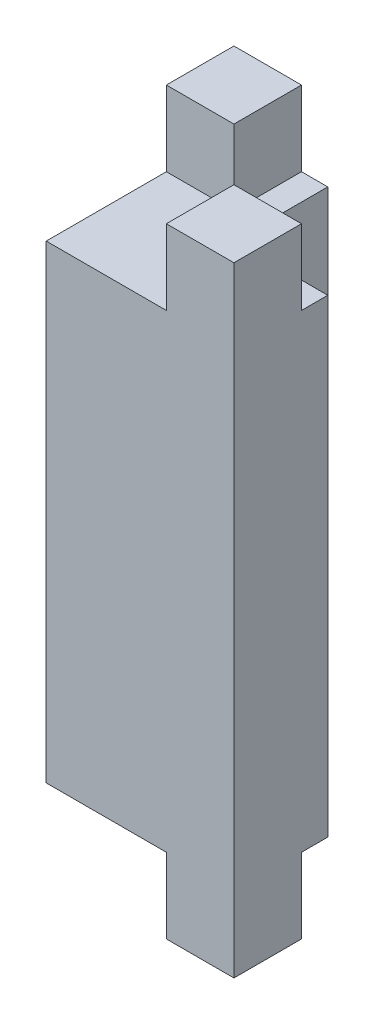
SolidWorks part; units mm, degrees
ref_plane "Front Plane" through (0, 0, 0) normal (0, 0, 1) x (1, 0, 0)
ref_plane "Top Plane" through (0, 0, 0) normal (0, 1, 0) x (1, 0, 0)
ref_plane "Right Plane" through (0, 0, 0) normal (1, 0, 0) x (0, 0, -1)
sketch "Sketch12" plane through (0, 0, 0) normal (0, 1, 0) x (1, 0, 0)
  line L0 (-5, -5) -> (5, -5)
  line L1 (-5, -5) -> (-5, 0)
  line L2 (0, 0) -> (5, 0)
  line L3 (5, -5) -> (5, 0)
  line L4 (-5, 0) -> (-5, 5)
  line L5 (-5, 5) -> (0, 5)
  line L6 (0, 0) -> (0, 5)
  dimension "D1" = 5
  dimension "D2" = 10
  dimension "D3" = 5
  dimension "D4" = 5
extrude "Boss-Extrude2" add sketch "Sketch12" along normal blind 25
sketch "Sketch13" plane through (0, 0, 0) normal (0, 1, 0) x (1, 0, 0)
  line L1 (-1.4, 5) -> (-5, 5)
  line L2 (-1.4, 5) -> (-1.4, 1.4)
  line L3 (-1.4, 1.4) -> (-5, 1.4)
  line L4 (-5, 5) -> (-5, 1.4)
  line L5 (5, -1.4) -> (1.4, -1.4)
  line L6 (5, -1.4) -> (5, -5)
  line L7 (5, -5) -> (1.4, -5)
  line L8 (1.4, -1.4) -> (1.4, -5)
  line L13 (-5, 5) -> (-5, -5) construction
  line L15 (-5, -5) -> (5, -5) construction
  point P10 (0, 0)
  point P11 (0, 0)
  point P12 (0, 0)
  point P13 (0, 0)
  point P19 (0, 0)
  point P20 (0, 0)
  dimension "D1" = 3.6
  dimension "D2" = 3.6
  dimension "D3" = 3.6
  dimension "D4" = 3.6
  dimension "D5" = 0
  dimension "D6" = 0
extrude "Boss-Extrude3" add sketch "Sketch13" against normal blind 4
sketch "Sketch15" plane through (0, 25, 0) normal (0, 1, 0) x (1, 0, 0)
  line L1 (-1.4, 5) -> (-5, 5)
  line L2 (-1.4, 5) -> (-1.4, 1.4)
  line L3 (-1.4, 1.4) -> (-5, 1.4)
  line L4 (-5, 5) -> (-5, 1.4)
  line L5 (5, -1.4) -> (1.4, -1.4)
  line L6 (5, -1.4) -> (5, -5)
  line L7 (5, -5) -> (1.4, -5)
  line L8 (1.4, -1.4) -> (1.4, -5)
  line L16 (5, -5) -> (5, 0) construction
  line L17 (0, 5) -> (-5, 5) construction
  line L19 (-5, 5) -> (-5, -5) construction
  line L21 (-5, -5) -> (5, -5) construction
  point P4 (0, 0)
  point P16 (0, 0)
  point P17 (0, 0)
  point P18 (0, 0)
  point P19 (0, 0)
  point P22 (0, 0)
  dimension "D1" = 3.6
  dimension "D2" = 3.6
  dimension "D3" = 3.6
  dimension "D4" = 0
  dimension "D5" = 3.6
  dimension "D6" = 0
  dimension "D7" = 0
  dimension "D8" = 0
extrude "Boss-Extrude4" add sketch "Sketch15" along normal blind 4
